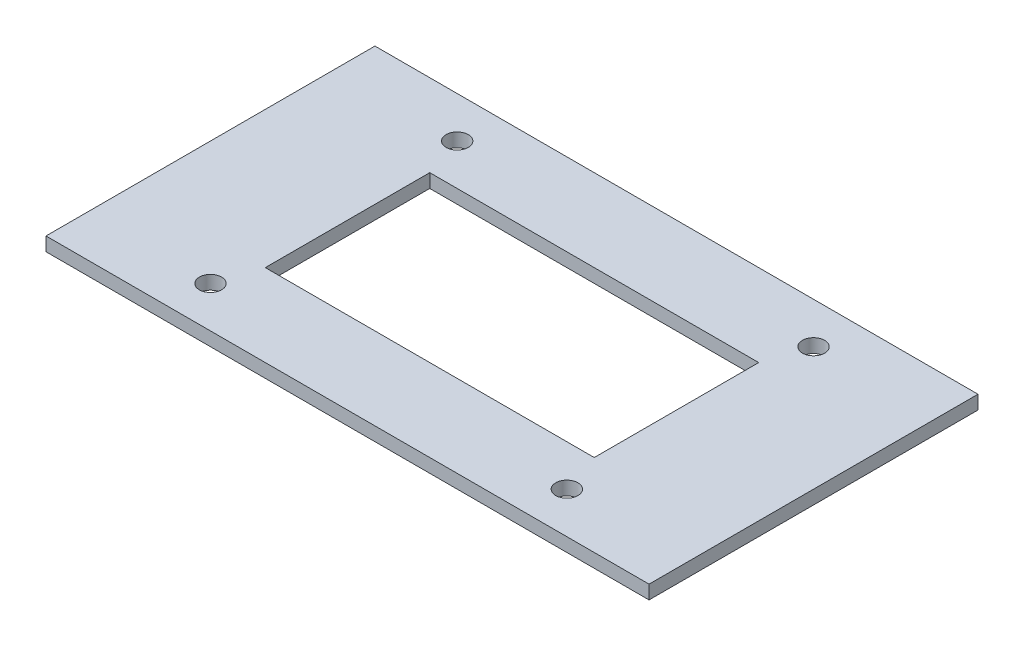
SolidWorks part; units mm, degrees
ref_plane "Front Plane" through (0, 0, 0) normal (0, 0, 1) x (1, 0, 0)
ref_plane "Top Plane" through (0, 0, 0) normal (0, 1, 0) x (1, 0, 0)
ref_plane "Right Plane" through (0, 0, 0) normal (1, 0, 0) x (0, 0, -1)
sketch "Sketch1" plane through (0, 0, 0) normal (0, 1, 0) x (1, 0, 0)
  line L1 (-59.5002, 46.8644) -> (499.2998, 46.8644)
  line L2 (-59.5002, 46.8644) -> (-59.5002, -257.9356)
  line L3 (-59.5002, -257.9356) -> (499.2998, -257.9356)
  line L4 (499.2998, 46.8644) -> (499.2998, -257.9356)
  dimension "D1" = 558.8
  dimension "D2" = 304.8
extrude "Boss-Extrude1" add sketch "Sketch1" along normal blind 12.7
sketch "Sketch2" plane through (0, 12.7, 0) normal (0, 1, 0) x (1, 0, 0)
  line L0 (-59.5002, 46.8644) -> (-59.5002, -257.9356) construction
  line L6 (67.4998, -181.7356) -> (372.2998, -181.7356)
  line L7 (67.4998, -181.7356) -> (67.4998, -29.3356)
  line L8 (67.4998, -29.3356) -> (372.2998, -29.3356)
  line L9 (372.2998, -181.7356) -> (372.2998, -29.3356)
  line L11 (372.2998, -29.3356) -> (372.2998, -181.7356) construction
  line L12 (372.2998, -181.7356) -> (67.4998, -181.7356) construction
  line L13 (67.4998, -181.7356) -> (67.4998, -29.3356) construction
  dimension "D1" = 304.8
  dimension "D2" = 152.4
  dimension "D3" = 127
extrude "Cut-Extrude1" cut sketch "Sketch2" against normal blind 12.7
sketch "Sketch4" plane through (0, 12.7, 0) normal (0, 1, 0) x (1, 0, 0)
  line L1 (67.4998, -181.7356) -> (372.2998, -181.7356) construction
  line L4 (372.2998, -29.3356) -> (67.4998, -29.3356) construction
  line L7 (-59.5002, 46.8644) -> (-59.5002, -257.9356) construction
  circle A0 centre (54.7998, 8.7644) radius 10.287
  circle A1 centre (384.9998, 8.7644) radius 10.287
  circle A2 centre (54.7998, -219.8356) radius 10.287
  circle A3 centre (384.9998, -219.8356) radius 10.287
  dimension "D1" = 20.574
  dimension "D2" = 20.574
  dimension "D3" = 20.574
  dimension "D4" = 20.574
  dimension "D7" = 330.2
  dimension "D9" = 114.3
  dimension "D10" = 38.1
  dimension "D11" = 38.1
  dimension "D5" = 330.2
  dimension "D6" = 38.1
  dimension "D8" = 38.1
extrude "Cut-Extrude2" cut sketch "Sketch4" against normal blind 12.7
